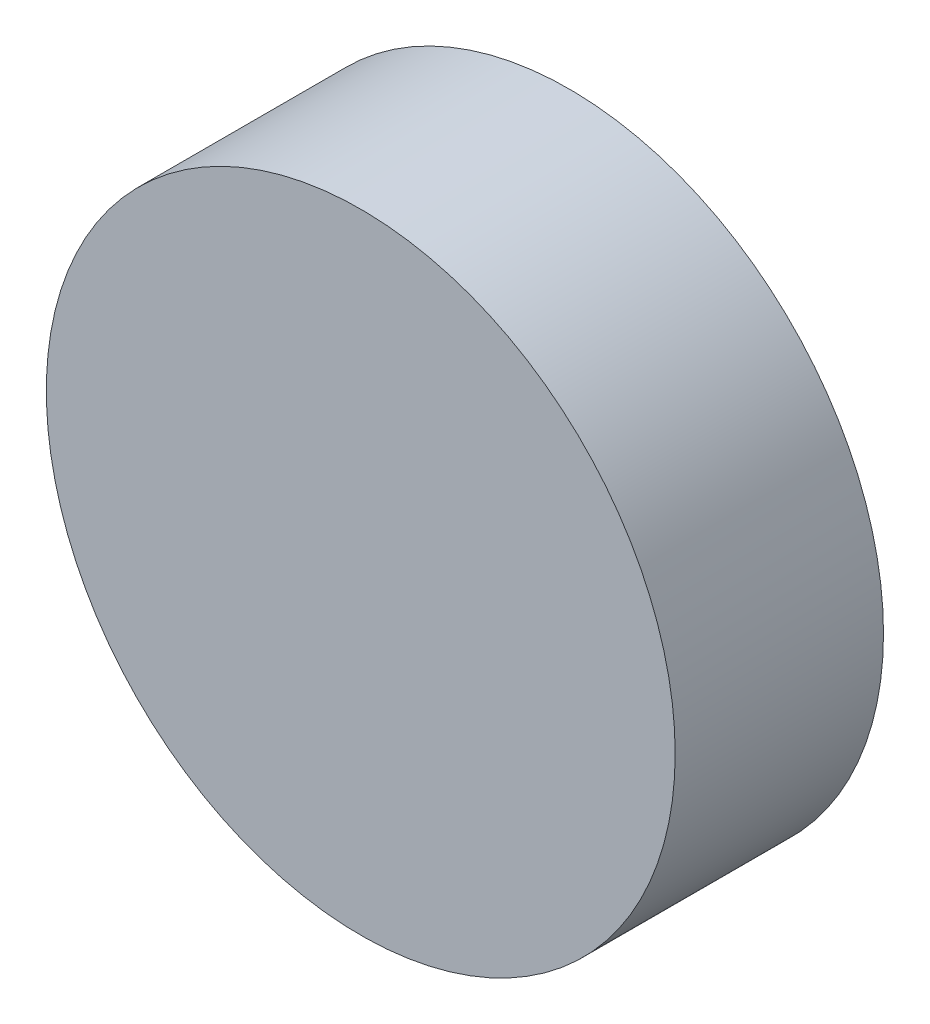
SolidWorks part; units mm, degrees
ref_plane "前视基准面" through (0, 0, 0) normal (0, 0, 1) x (1, 0, 0)
ref_plane "上视基准面" through (0, 0, 0) normal (0, 1, 0) x (1, 0, 0)
ref_plane "右视基准面" through (0, 0, 0) normal (1, 0, 0) x (0, 0, -1)
sketch "草图1" plane through (0, 0, 0) normal (0, 0, 1) x (1, 0, 0)
  circle A0 centre (0, 0) radius 4
  dimension "D1" = 8
extrude "凸台-拉伸1" add sketch "草图1" along normal blind 2.65
